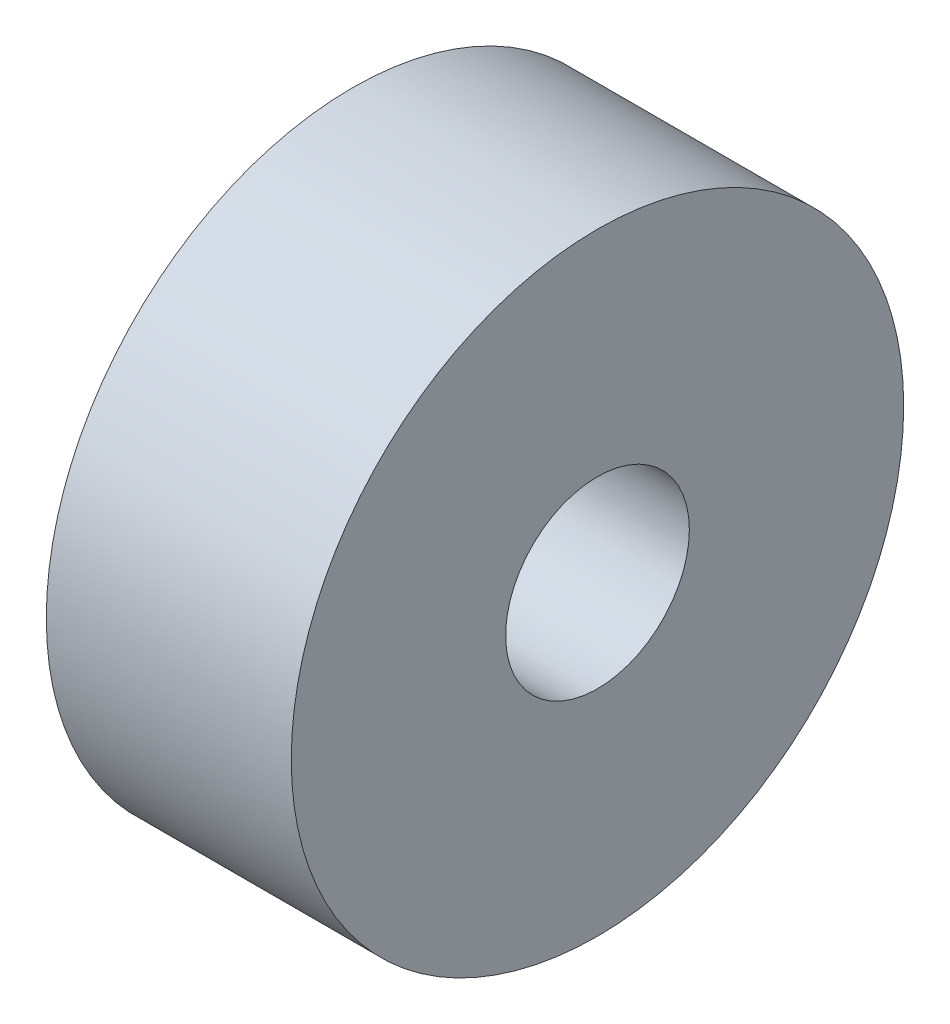
SolidWorks part; units mm, degrees
ref_plane "Front Plane" through (0, 0, 0) normal (0, 0, 1) x (1, 0, 0)
ref_plane "Top Plane" through (0, 0, 0) normal (0, 1, 0) x (1, 0, 0)
ref_plane "Right Plane" through (0, 0, 0) normal (1, 0, 0) x (0, 0, -1)
sketch "Sketch1" plane through (0, 0, 0) normal (1, 0, 0) x (0, 0, -1)
  circle A0 centre (0, 0) radius 1.5
  circle A1 centre (0, 0) radius 5
extrude "Boss-Extrude1" add sketch "Sketch1" along normal blind 4
